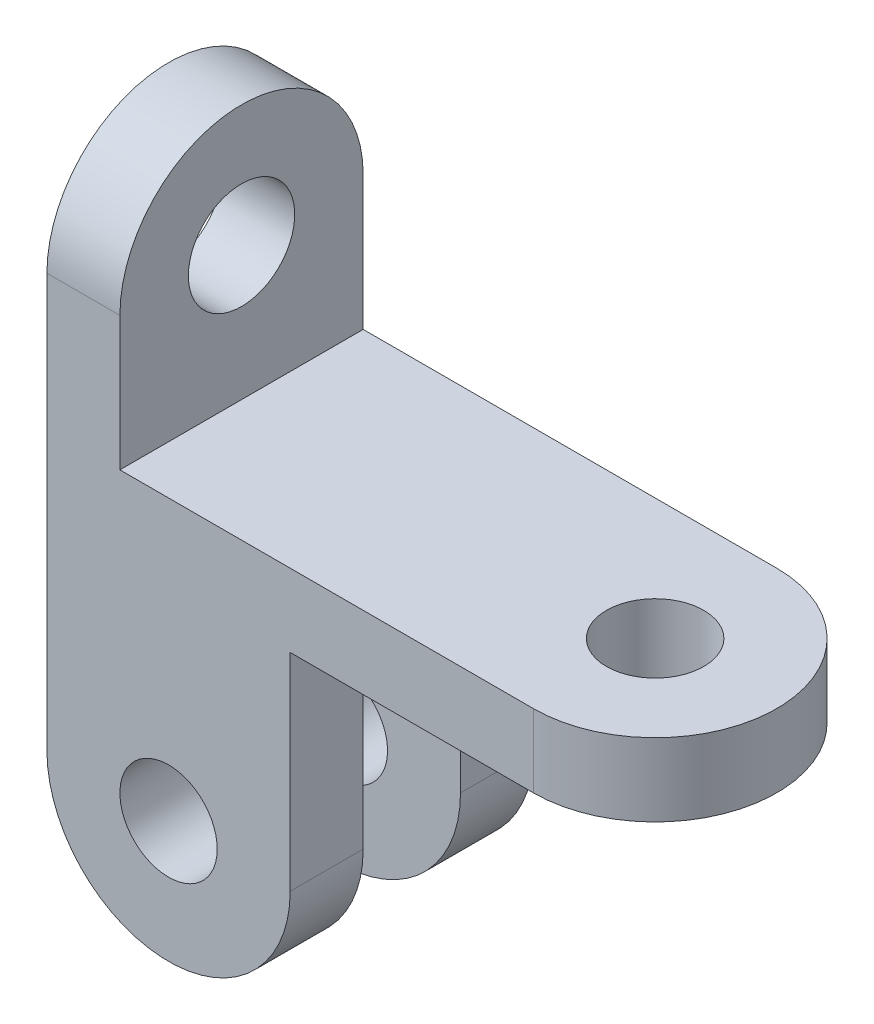
SolidWorks part; units mm, degrees
ref_plane "Front Plane" through (0, 0, 0) normal (0, 0, 1) x (1, 0, 0)
ref_plane "Top Plane" through (0, 0, 0) normal (0, 1, 0) x (1, 0, 0)
ref_plane "Right Plane" through (0, 0, 0) normal (1, 0, 0) x (0, 0, -1)
sketch "Sketch1" plane through (0, 0, 0) normal (0, 1, 0) x (1, 0, 0)
  line L1 (-64.7154, 17.8049) -> (15.2846, 17.8049)
  line L2 (-64.7154, 17.8049) -> (-64.7154, -22.1951)
  line L3 (-64.7154, -22.1951) -> (15.2846, -22.1951)
  line L5 (-64.7154, 17.8049) -> (-0.7154, -14.1951) construction
  line L6 (-64.7154, -22.1951) -> (-24.7154, -2.1951) construction
  arc A0 (15.2846, -22.1951) -> (15.2846, 17.8049) centre (15.2846, -2.1951) ccw
  circle A1 centre (15.2846, -2.1951) radius 8
  point P0 (-24.7154, -2.1951)
  dimension "D3" = 40
  dimension "D4" = 16
  dimension "D1" = 80
  dimension "D2" = 40
extrude "Boss-Extrude2" add sketch "Sketch1" along normal blind 12
sketch "Sketch3" plane through (-64.7154, 0, 0) normal (-1, 0, 0) x (0, 0, 1)
  line L0 (2.1951, 12) -> (2.1951, 14) construction
  line L1 (-17.8049, 12) -> (22.1951, 12) construction
  line L2 (-17.8049, 34) -> (-17.8049, 12)
  line L3 (22.1951, 34) -> (22.1951, 12)
  arc A0 (22.1951, 34) -> (-17.8049, 34) centre (2.1951, 34) ccw
  circle A1 centre (2.1951, 34) radius 8.7426
  dimension "D2" = 40
  dimension "D1" = 22
extrude "Boss-Extrude3" add sketch "Sketch3" against normal blind 12
sketch "Sketch4" plane through (0, 0, -17.8049) normal (0, 0, -1) x (-1, 0, 0)
  line L0 (64.7154, 0) -> (64.7154, -34)
  line L2 (24.7154, -34) -> (24.7154, 0)
  line L3 (-15.2846, 0) -> (64.7154, 0) construction
  line L4 (24.7154, 0) -> (64.7154, 0)
  arc A0 (24.7154, -34) -> (64.7154, -34) centre (44.7154, -34) ccw
  circle A1 centre (44.7154, -34) radius 8
  dimension "D3" = 40
  dimension "D4" = 16
  dimension "D6" = 20
  dimension "D1" = 34
  dimension "D2" = 20
  dimension "D5" = 34
extrude "Boss-Extrude4" add sketch "Sketch4" against normal blind 12
sketch "Sketch5" plane through (0, 0, 22.1951) normal (0, 0, 1) x (1, 0, 0)
  line L0 (-64.7154, 0) -> (-64.7154, -34)
  line L2 (-24.7154, 0) -> (-24.7154, -34)
  line L3 (-24.7154, 0) -> (-64.7154, 0)
  arc A0 (-64.7154, -34) -> (-24.7154, -34) centre (-44.7154, -34) ccw
  circle A1 centre (-44.7154, -34) radius 8
  dimension "D1" = 16
extrude "Boss-Extrude5" add sketch "Sketch5" against normal blind 12
